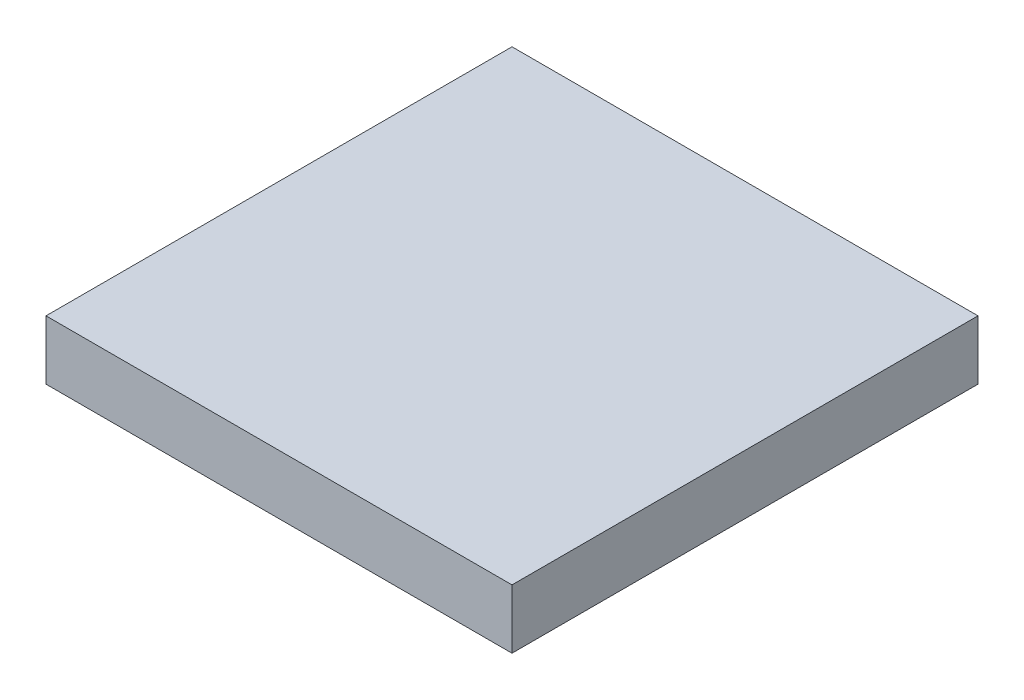
SolidWorks part; units mm, degrees
ref_plane "Front Plane" through (0, 0, 0) normal (0, 0, 1) x (1, 0, 0)
ref_plane "Top Plane" through (0, 0, 0) normal (0, 1, 0) x (1, 0, 0)
ref_plane "Right Plane" through (0, 0, 0) normal (1, 0, 0) x (0, 0, -1)
sketch "Sketch1" plane through (0, 0, 0) normal (0, 1, 0) x (1, 0, 0)
  line L1 (-50, -50) -> (50, -50)
  line L2 (-50, -50) -> (-50, 50)
  line L3 (-50, 50) -> (50, 50)
  line L4 (50, -50) -> (50, 50)
  line L5 (-50, -50) -> (50, 50) construction
  line L6 (-50, 50) -> (50, -50) construction
  point P0 (0, 0)
  dimension "D1" = 100
  dimension "D2" = 100
extrude "Boss-Extrude1" add sketch "Sketch1" along normal blind 12.7
